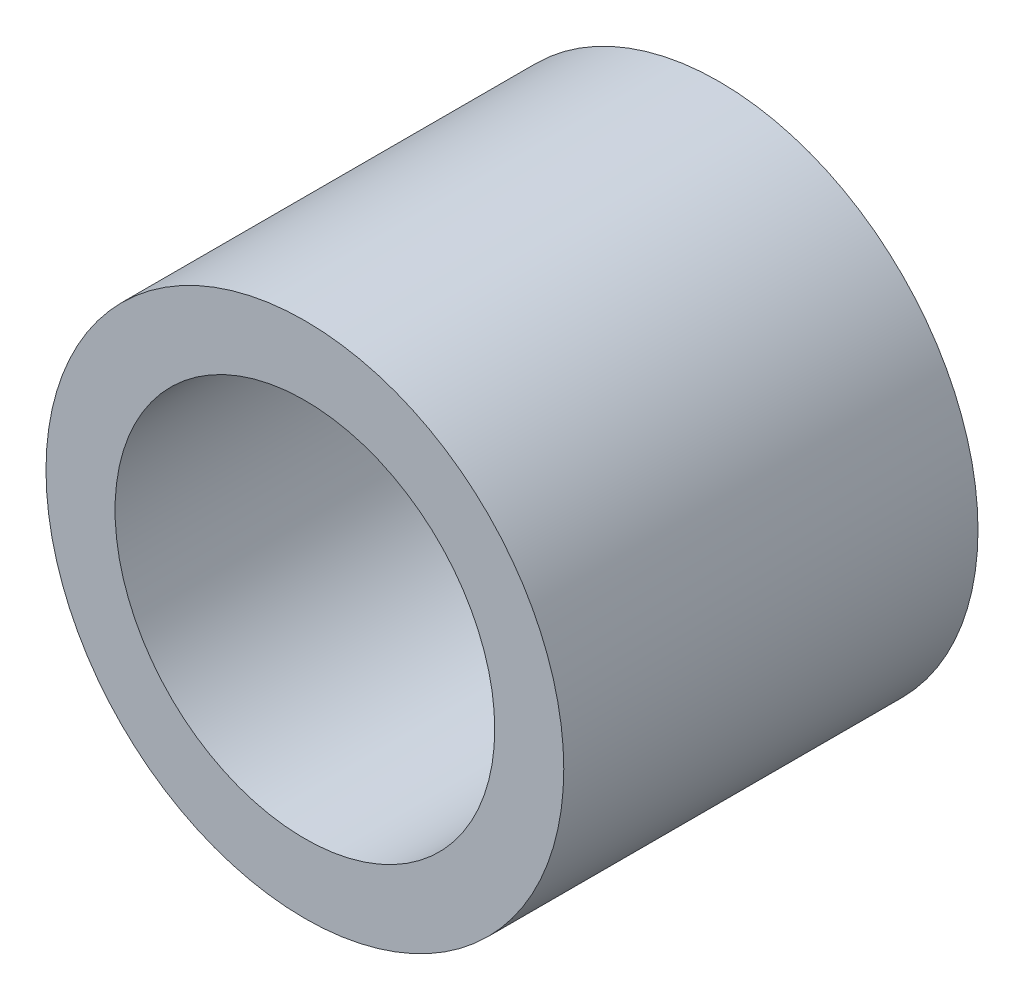
SolidWorks part; units mm, degrees
ref_plane "Front Plane" through (0, 0, 0) normal (0, 0, 1) x (1, 0, 0)
ref_plane "Top Plane" through (0, 0, 0) normal (0, 1, 0) x (1, 0, 0)
ref_plane "Right Plane" through (0, 0, 0) normal (1, 0, 0) x (0, 0, -1)
sketch "Sketch1" plane through (0, 0, 0) normal (0, 0, 1) x (1, 0, 0)
  circle A0 centre (0, 0) radius 3.75
  circle A1 centre (0, 0) radius 2.75
  dimension "D1" = 7.5
  dimension "D2" = 1
extrude "Boss-Extrude1" add sketch "Sketch1" along normal blind 6
